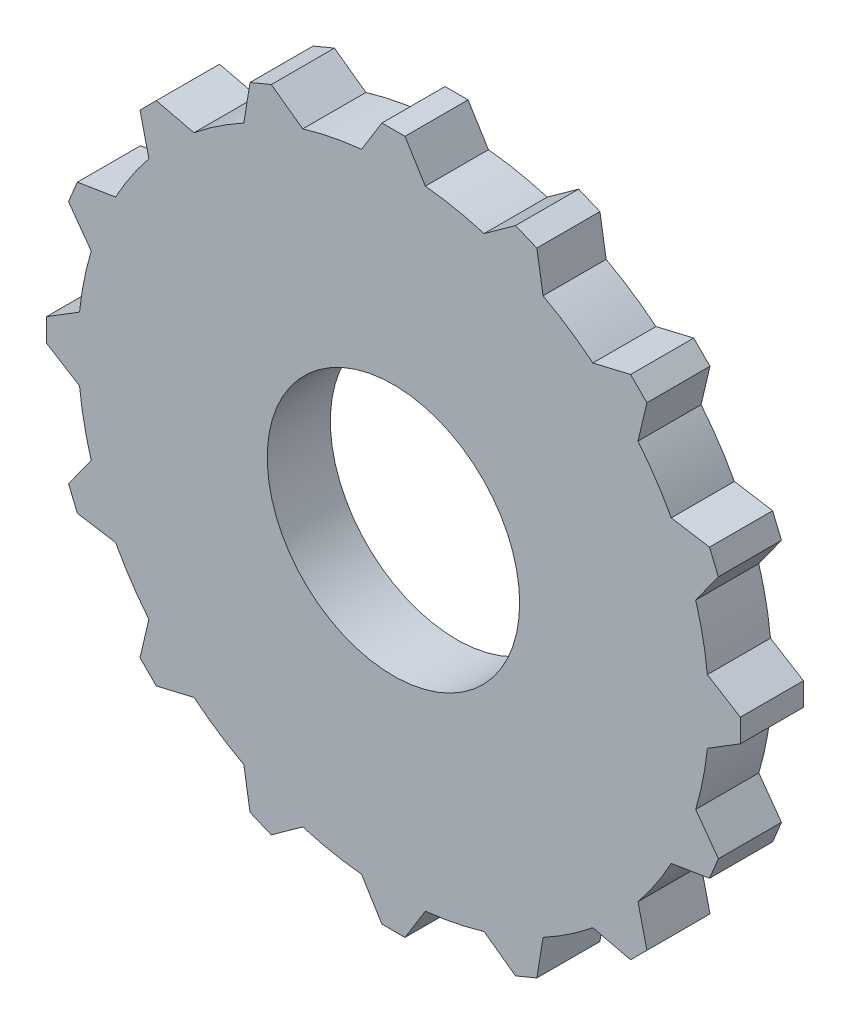
SolidWorks part; units mm, degrees
ref_plane "Front Plane" through (0, 0, 0) normal (0, 0, 1) x (1, 0, 0)
ref_plane "Top Plane" through (0, 0, 0) normal (0, 1, 0) x (1, 0, 0)
ref_plane "Right Plane" through (0, 0, 0) normal (1, 0, 0) x (0, 0, -1)
sketch "Sketch1" plane through (0, 0, 0) normal (0, 0, 1) x (1, 0, 0)
  line L0 (1.8263, 54.9697) -> (-1.8263, 54.9697)
  line L3 (5.0555, 49.7438) -> (1.8263, 54.9697)
  line L6 (0, -60.5611) -> (0, 60.5611) construction
  line L9 (-5.0555, 49.7438) -> (-1.8263, 54.9697)
  line L10 (14.3654, 47.8919) -> (19.3487, 51.4843)
  line L11 (22.7233, 50.0865) -> (19.3487, 51.4843)
  line L12 (23.7068, 44.0226) -> (22.7233, 50.0865)
  line L13 (31.5993, 38.749) -> (37.578, 40.1608)
  line L14 (40.1608, 37.578) -> (37.578, 40.1608)
  line L15 (38.749, 31.5993) -> (40.1608, 37.578)
  line L16 (44.0226, 23.7068) -> (50.0865, 22.7233)
  line L17 (51.4843, 19.3487) -> (50.0865, 22.7233)
  line L18 (47.8919, 14.3654) -> (51.4843, 19.3487)
  line L19 (49.7438, 5.0555) -> (54.9697, 1.8263)
  line L20 (54.9697, -1.8263) -> (54.9697, 1.8263)
  line L21 (49.7438, -5.0555) -> (54.9697, -1.8263)
  line L22 (47.8919, -14.3654) -> (51.4843, -19.3487)
  line L23 (50.0865, -22.7233) -> (51.4843, -19.3487)
  line L24 (44.0226, -23.7068) -> (50.0865, -22.7233)
  line L25 (38.749, -31.5993) -> (40.1608, -37.578)
  line L26 (37.578, -40.1608) -> (40.1608, -37.578)
  line L27 (31.5993, -38.749) -> (37.578, -40.1608)
  line L28 (23.7068, -44.0226) -> (22.7233, -50.0865)
  line L29 (19.3487, -51.4843) -> (22.7233, -50.0865)
  line L30 (14.3654, -47.8919) -> (19.3487, -51.4843)
  line L31 (5.0555, -49.7438) -> (1.8263, -54.9697)
  line L32 (-1.8263, -54.9697) -> (1.8263, -54.9697)
  line L33 (-5.0555, -49.7438) -> (-1.8263, -54.9697)
  line L34 (-14.3654, -47.8919) -> (-19.3487, -51.4843)
  line L35 (-22.7233, -50.0865) -> (-19.3487, -51.4843)
  line L36 (-23.7068, -44.0226) -> (-22.7233, -50.0865)
  line L37 (-31.5993, -38.749) -> (-37.578, -40.1608)
  line L38 (-40.1608, -37.578) -> (-37.578, -40.1608)
  line L39 (-38.749, -31.5993) -> (-40.1608, -37.578)
  line L40 (-44.0226, -23.7068) -> (-50.0865, -22.7233)
  line L41 (-51.4843, -19.3487) -> (-50.0865, -22.7233)
  line L42 (-47.8919, -14.3654) -> (-51.4843, -19.3487)
  line L43 (-49.7438, -5.0555) -> (-54.9697, -1.8263)
  line L44 (-54.9697, 1.8263) -> (-54.9697, -1.8263)
  line L45 (-49.7438, 5.0555) -> (-54.9697, 1.8263)
  line L46 (-47.8919, 14.3654) -> (-51.4843, 19.3487)
  line L47 (-50.0865, 22.7233) -> (-51.4843, 19.3487)
  line L48 (-44.0226, 23.7068) -> (-50.0865, 22.7233)
  line L49 (-38.749, 31.5993) -> (-40.1608, 37.578)
  line L50 (-37.578, 40.1608) -> (-40.1608, 37.578)
  line L51 (-31.5993, 38.749) -> (-37.578, 40.1608)
  line L52 (-23.7068, 44.0226) -> (-22.7233, 50.0865)
  line L53 (-19.3487, 51.4843) -> (-22.7233, 50.0865)
  line L54 (-14.3654, 47.8919) -> (-19.3487, 51.4843)
  circle A0 centre (0, 0) radius 20
  circle A1 centre (0, 0) radius 40
  arc A2 (-23.7068, 44.0226) -> (-31.5993, 38.749) centre (0, 0) ccw
  arc A4 (-38.749, 31.5993) -> (-44.0226, 23.7068) centre (0, 0) ccw
  arc A5 (-47.8919, 14.3654) -> (-49.7438, 5.0555) centre (0, 0) ccw
  arc A6 (-49.7438, -5.0555) -> (-47.8919, -14.3654) centre (0, 0) ccw
  arc A7 (-44.0226, -23.7068) -> (-38.749, -31.5993) centre (0, 0) ccw
  arc A8 (-31.5993, -38.749) -> (-23.7068, -44.0226) centre (0, 0) ccw
  arc A9 (-14.3654, -47.8919) -> (-5.0555, -49.7438) centre (0, 0) ccw
  arc A10 (5.0555, -49.7438) -> (14.3654, -47.8919) centre (0, 0) ccw
  arc A11 (23.7068, -44.0226) -> (31.5993, -38.749) centre (0, 0) ccw
  arc A12 (38.749, -31.5993) -> (44.0226, -23.7068) centre (0, 0) ccw
  arc A13 (47.8919, -14.3654) -> (49.7438, -5.0555) centre (0, 0) ccw
  arc A14 (49.7438, 5.0555) -> (47.8919, 14.3654) centre (0, 0) ccw
  arc A15 (44.0226, 23.7068) -> (38.749, 31.5993) centre (0, 0) ccw
  arc A16 (31.5993, 38.749) -> (23.7068, 44.0226) centre (0, 0) ccw
  arc A17 (14.3654, 47.8919) -> (5.0555, 49.7438) centre (0, 0) ccw
  arc A18 (-5.0555, 49.7438) -> (-14.3654, 47.8919) centre (0, 0) ccw
  point P9 (0, 54.9697)
  point P74 (0, 0)
  point P92 (0, 0)
  dimension "D1" = 16
extrude "Boss-Extrude1" add sketch "Sketch1" along normal blind 10 contours L9 A18 L54 L53 L52 A2 L51 L50 L49 A4 L48 L47 L46 A5 L45 L44 L43 A6 L42 L41 L40 A7 L39 L38 L37 A8 L36 L35 L34 A9 L33 L32 L31 A10 L30 L29 L28 A11 L27 L26 L25 A12 L24 L23 L22 A13 L21 L20 L19 A14 L18 | A1 A0
sketch "Sketch2" plane through (0, 0, 0) normal (0, 0, 1) x (1, 0, 0)
  line L0 (-19.3487, 51.4843) -> (0, 0)
  line L1 (-23.7068, 44.0226) -> (0, 0)
  line L2 (-22.7233, 50.0865) -> (0, 0)
  line L3 (-14.3654, 47.8919) -> (0, 0)
  line L4 (-5.0555, 49.7438) -> (5.0555, 49.7438)
  line L5 (-1.8263, 54.9697) -> (1.8263, 54.9697)
  line L6 (44.0226, 23.7068) -> (44.0226, -23.7068)
  line L7 (44.0226, 23.7068) -> (0, 0)
  line L8 (44.0226, -23.7068) -> (0, 0)
  line L9 (0, 0) -> (44.0226, 0)
  line L10 (0, 0) -> (38.749, 31.5993)
  line L11 (0, 0) -> (38.749, -31.5993)
  line L12 (38.749, 31.5993) -> (38.749, -31.5993)
  line L13 (0, 0) -> (38.749, 0)
  line L14 (38.749, 0) -> (0, 0)
  line L15 (0, 8.6101) -> (38.749, 8.6101)
  line L16 (0, -5.5) -> (0, 5.5) construction
  circle A2 centre (0, 0) radius 55
  dimension "D1" = 55
  dimension "D2" = 3.806
  dimension "D3" = 11.606
  dimension "D4" = 10.1111
  dimension "D5" = 3.6526
  dimension "D6" = 5.2259
  dimension "D7" = 47.4137
  dimension "D8" = 56.606
  dimension "D9" = 44.0226
  dimension "D10" = 78.394
  dimension "D11" = 63.1987
  dimension "D12" = 38.749
